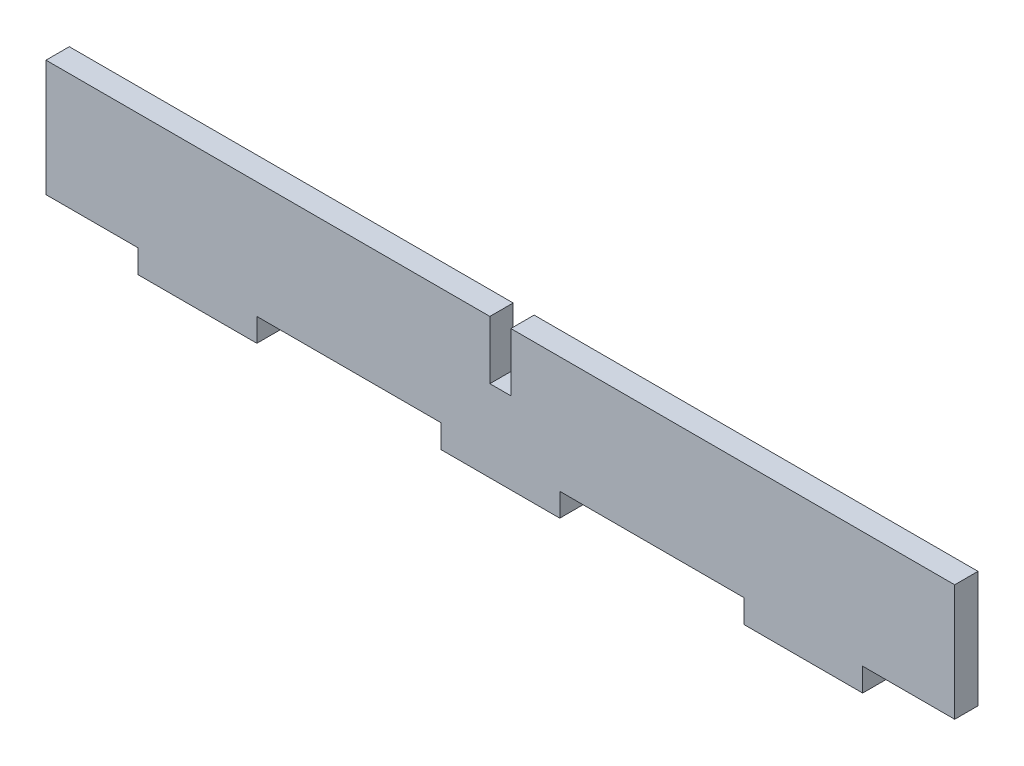
SolidWorks part; units mm, degrees
ref_plane "前基準面" through (0, 0, 0) normal (0, 0, 1) x (1, 0, 0)
ref_plane "上基準面" through (0, 0, 0) normal (0, 1, 0) x (1, 0, 0)
ref_plane "右基準面" through (0, 0, 0) normal (1, 0, 0) x (0, 0, -1)
sketch "草圖1" plane through (0, 0, 0) normal (0, 0, 1) x (1, 0, 0)
  line L0 (0, 0) -> (0, 19.9222) construction
  line L1 (-39, 2) -> (-31.1, 2)
  line L2 (-39, 2) -> (-39, 12)
  line L3 (-39, 12) -> (-0.9, 12)
  line L4 (39, 2) -> (39, 12)
  line L5 (-20.9, 2) -> (-5.1, 2)
  line L6 (31.1, 2) -> (39, 2)
  line L7 (-31.1, 2) -> (-31.1, 0)
  line L8 (-31.1, 0) -> (-20.9, 0)
  line L9 (-20.9, 2) -> (-20.9, 0)
  line L10 (0.9, 12) -> (39, 12)
  line L11 (20.9, 2) -> (20.9, 0)
  line L12 (20.9, 0) -> (31.1, 0)
  line L13 (31.1, 2) -> (31.1, 0)
  line L14 (0, 0) -> (-12.6558, 0) construction
  line L15 (-0.9, 12) -> (-0.9, 7)
  line L16 (-0.9, 7) -> (0.9, 7)
  line L17 (0.9, 12) -> (0.9, 7)
  line L18 (5.1, 2) -> (20.9, 2)
  line L20 (-5.1, 2) -> (-5.1, 0)
  line L21 (-5.1, 0) -> (5.1, 0)
  line L22 (5.1, 2) -> (5.1, 0)
  dimension "D1" = 78
  dimension "D2" = 10
  dimension "D3" = 2
  dimension "D4" = 41.8
  dimension "D5" = 62.2
  dimension "D6" = 2
  dimension "D7" = 1.8
  dimension "D8" = 5
  dimension "D9" = 10.2
  dimension "D10" = 2
extrude "填料-伸長1" add sketch "草圖1" along normal blind 2
